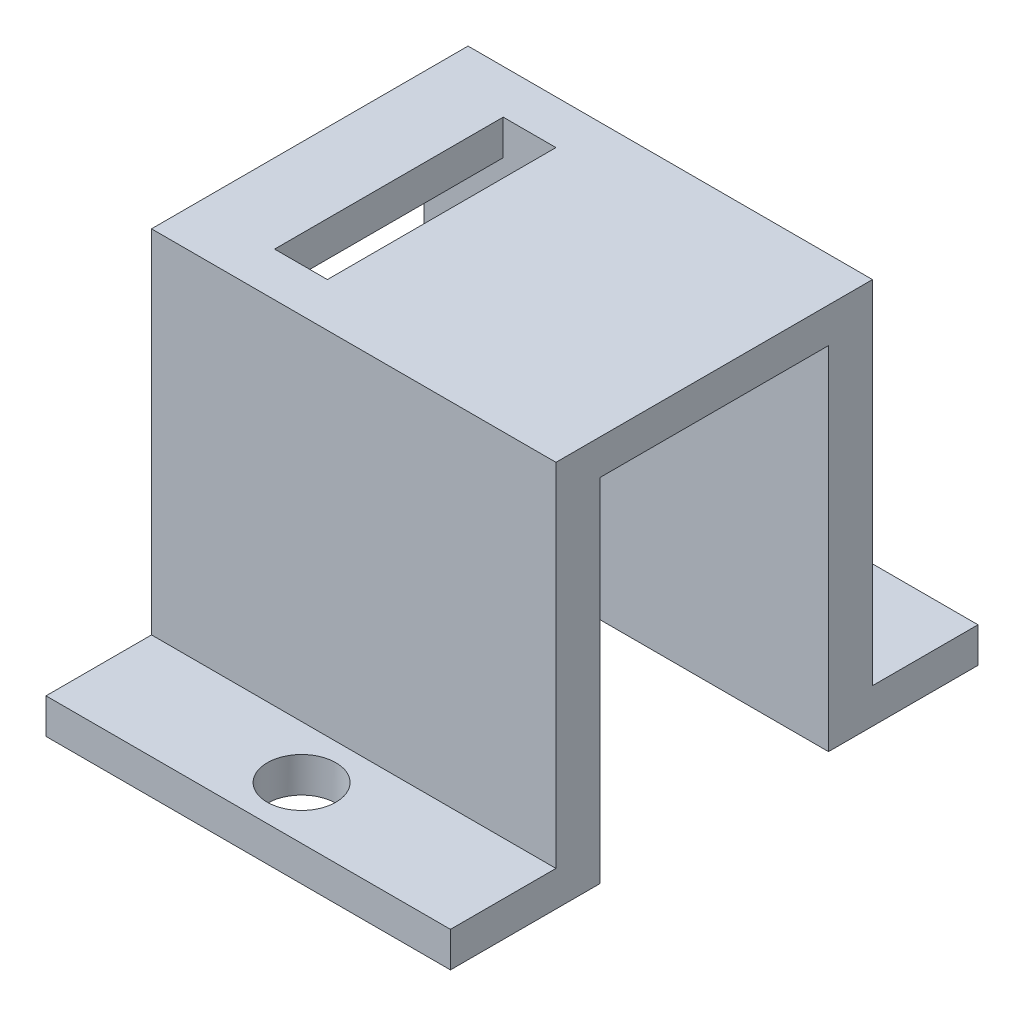
SolidWorks part; units mm, degrees
ref_plane "Plan de face" through (0, 0, 0) normal (0, 0, 1) x (1, 0, 0)
ref_plane "Plan de dessus" through (0, 0, 0) normal (0, 1, 0) x (1, 0, 0)
ref_plane "Plan de droite" through (0, 0, 0) normal (1, 0, 0) x (0, 0, -1)
sketch "Esquisse1" plane through (0, 0, 0) normal (0, 1, 0) x (1, 0, 0)
  line L1 (0, 0) -> (23, 0)
  line L2 (0, 0) -> (0, 30)
  line L3 (0, 30) -> (23, 30)
  line L4 (23, 0) -> (23, 30)
  dimension "D1" = 23
  dimension "D2" = 30
extrude "Boss.-Extru.1" add sketch "Esquisse1" along normal blind 22
sketch "Esquisse2" plane through (0, 22, 0) normal (0, 1, 0) x (1, 0, 0)
  line L0 (23, 0) -> (23, 30) construction
  line L1 (0, 30) -> (23, 30)
  line L2 (0, 30) -> (0, 24)
  line L3 (0, 24) -> (23, 24)
  line L4 (23, 30) -> (23, 24)
  line L5 (-7.0201, 15) -> (30.3648, 15) construction
  line L6 (23, 0) -> (23, 6)
  line L7 (0, 6) -> (23, 6)
  line L8 (0, 0) -> (23, 0)
  line L9 (0, 0) -> (0, 6)
  line L10 (11.5, 30) -> (11.6724, 15) construction
  line L11 (11.6724, 15) -> (11.5, 0) construction
  line L12 (0, 0) -> (23, 0) construction
  line L13 (0, 27) -> (33.5217, 27) construction
  line L14 (0, 3) -> (30.3131, 3) construction
  dimension "D1" = 6
extrude "Enlèv. mat.-Extru.1" cut sketch "Esquisse2" against normal blind 20
hole_wizard "Dégagement M3.51" positions "Esquisse4" profile "Esquisse3" hole size "M3.5" standard "Iso"
sketch "Esquisse4" plane through (0, 2, 0) normal (0, 1, 0) x (1, 0, 0)
  line L0 (11.5, 30) -> (11.6724, 15) construction
  line L1 (11.6724, 15) -> (11.5, 0) construction
  line L2 (0, 3) -> (30.3131, 3) construction
  line L3 (0, 27) -> (33.5217, 27) construction
  point P0 (11.5345, 27)
  point P4 (11.5345, 3)
sketch "Esquisse3" plane through (11.5345, 2, -27) normal (1, 0, 0) x (0, 0, 1)
  line L0 (0, 0) -> (0, 6.1717)
  line L1 (0, 6.1717) -> (1.95, 5)
  line L2 (1.95, 5) -> (1.95, 0)
  line L5 (1.95, 0) -> (0, 0)
  line L10 (0, 6.1717) -> (-1.95, 5) construction
  line L11 (0, -6.35) -> (0, 107.95) construction
  dimension "Diamètre du perçage" = 3.9
  dimension "Profondeur du perçage" = 5
  dimension "Angle de pointe" = 118
sketch "Esquisse5" plane through (0, 22, 0) normal (0, 1, 0) x (1, 0, 0)
  line L1 (4.5, 21.5) -> (7.5, 21.5)
  line L2 (4.5, 21.5) -> (4.5, 8.5)
  line L3 (4.5, 8.5) -> (7.5, 8.5)
  line L4 (7.5, 21.5) -> (7.5, 8.5)
  line L6 (23, 6) -> (23, 24) construction
  line L8 (6, 6) -> (6, 8.5) construction
  line L9 (23, 6) -> (0, 6) construction
  line L10 (6, 21.5) -> (6, 24) construction
  line L11 (0, 24) -> (23, 24) construction
  dimension "D1" = 15.5
  dimension "D2" = 3
  dimension "D3" = 13
extrude "Enlèv. mat.-Extru.2" cut sketch "Esquisse5" against normal through all
sketch "Esquisse6" plane through (0, 0, 0) normal (0, -1, 0) x (1, 0, 0)
  line L1 (24.5, -21.5) -> (0, -21.5)
  line L2 (24.5, -21.5) -> (24.5, -8.5)
  line L3 (24.5, -8.5) -> (0, -8.5)
  line L4 (0, -21.5) -> (0, -8.5)
  line L7 (17.6928, -30) -> (17.6928, -21.5) construction
  line L9 (23, -30) -> (0, -30) construction
  line L10 (17.6928, -8.5) -> (17.6928, 0) construction
  line L11 (0, 0) -> (23, 0) construction
  dimension "D1" = 13
extrude "Enlèv. mat.-Extru.3" cut sketch "Esquisse6" against normal blind 20
